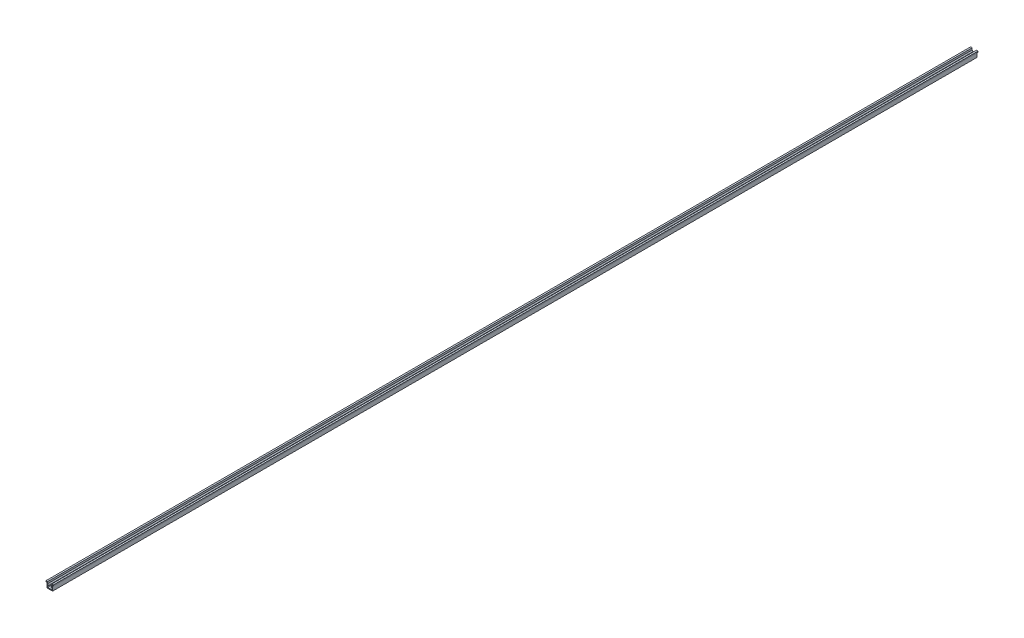
SolidWorks part; units mm, degrees
material "Пластик"
ref_plane "Спереди" through (0, 0, 0) normal (0, 0, 1) x (1, 0, 0)
ref_plane "Сверху" through (0, 0, 0) normal (0, 1, 0) x (1, 0, 0)
ref_plane "Справа" through (0, 0, 0) normal (1, 0, 0) x (0, 0, -1)
sketch "Эскиз1" plane through (0, 0, 0) normal (0, 0, 1) x (1, 0, 0)
  line L0 (3.1, 0) -> (-3.1, 0)
  line L1 (-3.1, 0) -> (-3.1, 5.3)
  line L2 (-3.1, 5.3) -> (-4, 5.3)
  line L3 (-4, 5.3) -> (-4, 6.3)
  line L4 (-4, 6.3) -> (-2.25, 6.3)
  line L5 (-2.25, 6.3) -> (-2.25, 4.3)
  line L6 (-2.25, 4.3) -> (-1.1893, 3.2393)
  line L7 (-1.1893, 3.2393) -> (-1.6136, 2.8151)
  line L8 (-1.6136, 2.8151) -> (-2.25, 3.4515)
  line L9 (-2.25, 3.4515) -> (-2.25, 0.85)
  line L10 (-2.25, 0.85) -> (2.25, 0.85)
  line L11 (0, 0.85) -> (0, 0) construction
  line L12 (2.25, 3.4515) -> (2.25, 0.85)
  line L13 (1.6136, 2.8151) -> (2.25, 3.4515)
  line L14 (1.1893, 3.2393) -> (1.6136, 2.8151)
  line L15 (2.25, 4.3) -> (1.1893, 3.2393)
  line L16 (2.25, 6.3) -> (2.25, 4.3)
  line L17 (4, 6.3) -> (2.25, 6.3)
  line L18 (4, 5.3) -> (4, 6.3)
  line L19 (3.1, 5.3) -> (4, 5.3)
  line L20 (3.1, 0) -> (3.1, 5.3)
  line L21 (-3.1, 2.65) -> (-2.25, 2.65) construction
  dimension "D1" = 6.2
  dimension "D2" = 8
  dimension "D3" = 4.5
  dimension "D4" = 6.3
  dimension "D5" = 1
  dimension "D6" = 135
  dimension "D7" = 1.5
  dimension "D8" = 0.6
  dimension "D9" = 2
extrude "Бобышка-Вытянуть1" add sketch "Эскиз1" along normal blind 1000
